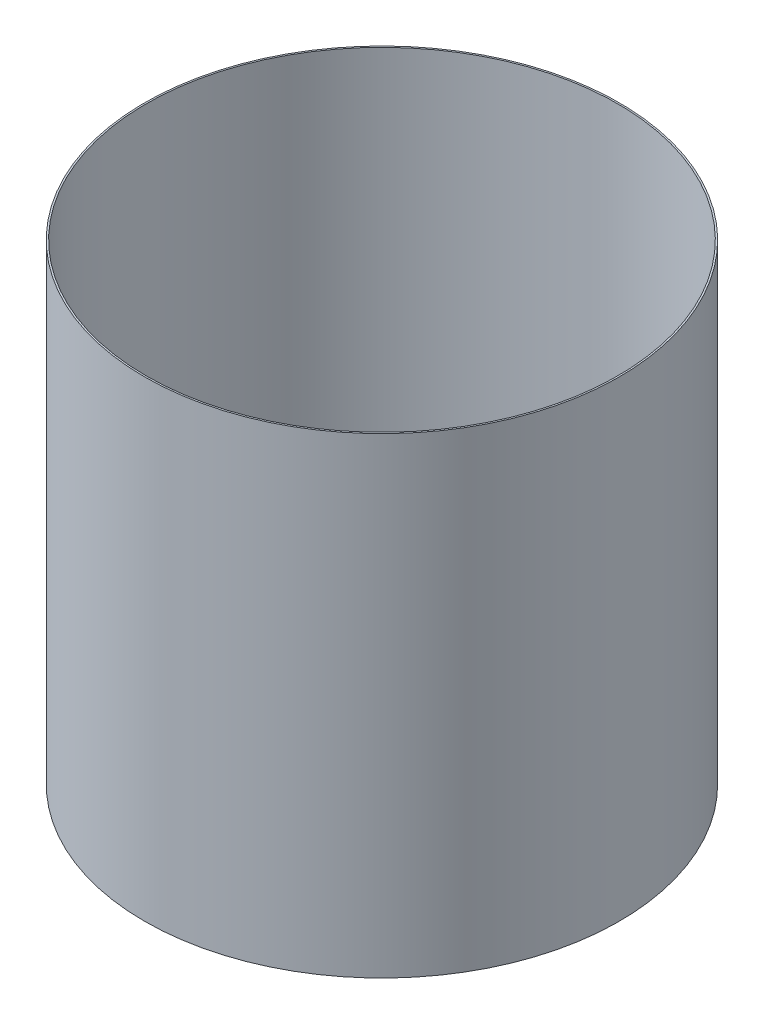
SolidWorks part; units mm, degrees
ref_plane "Front Plane" through (0, 0, 0) normal (0, 0, 1) x (1, 0, 0)
ref_plane "Top Plane" through (0, 0, 0) normal (0, 1, 0) x (1, 0, 0)
ref_plane "Right Plane" through (0, 0, 0) normal (1, 0, 0) x (0, 0, -1)
sketch "Sketch6" plane through (0, 0, 0) normal (0, 1, 0) x (1, 0, 0)
  circle A0 centre (0, 0) radius 228.6
  circle A1 centre (0, 0) radius 230.1875
  dimension "D1" = 457.2
  dimension "D2" = 460.375
extrude "Boss-Extrude1" add sketch "Sketch6" along normal mid plane 457.2
